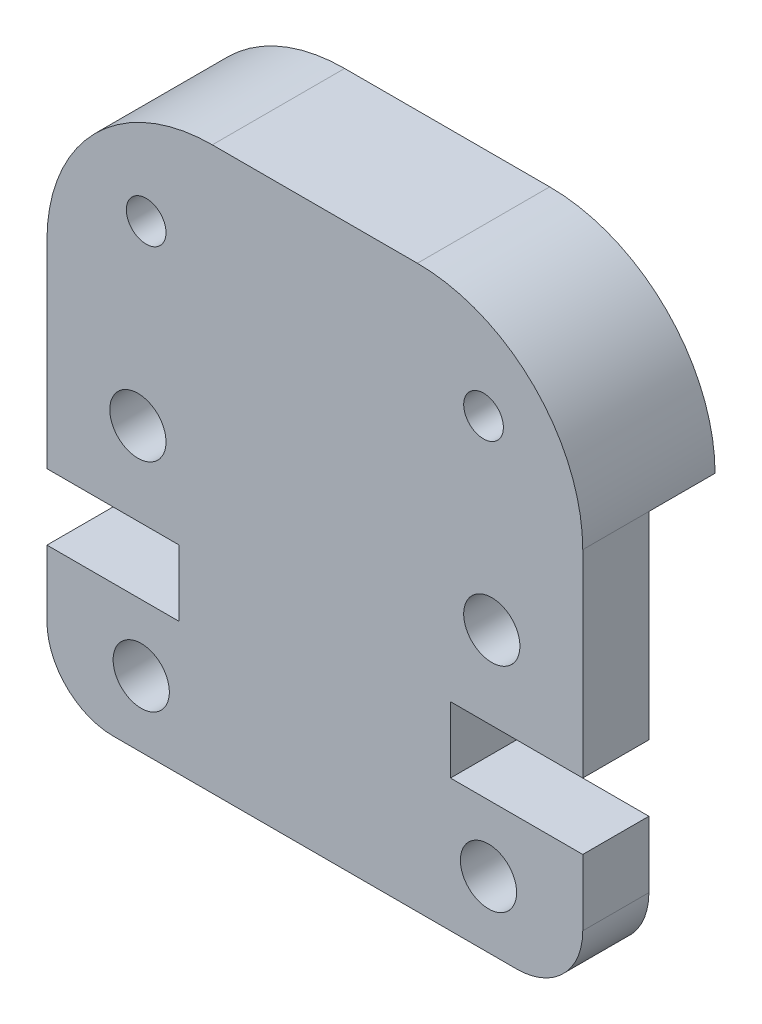
SolidWorks part; units mm, degrees
ref_plane "Front Plane" through (0, 0, 0) normal (0, 0, 1) x (1, 0, 0)
ref_plane "Top Plane" through (0, 0, 0) normal (0, 1, 0) x (1, 0, 0)
ref_plane "Right Plane" through (0, 0, 0) normal (1, 0, 0) x (0, 0, -1)
sketch "Sketch1" plane through (0, 0, 0) normal (0, 0, 1) x (1, 0, 0)
  line L0 (0, 16.98) -> (0, 0) construction
  line L1 (3.1, 16.98) -> (-3.1, 16.98)
  line L2 (6.1, 0) -> (-6.1, 0)
  line L3 (-8.1, 6) -> (-4.1, 6)
  line L4 (-4.1, 6) -> (-4.1, 4)
  line L5 (-4.1, 4) -> (-8.1, 4)
  line L6 (-8.1, 2) -> (-8.1, 4)
  line L7 (8.1, 11.98) -> (8.1, 6)
  line L8 (-8.1, 11.98) -> (-8.1, 6)
  line L24 (8.1, 2) -> (8.1, 4)
  line L27 (4.1, 4) -> (8.1, 4)
  line L30 (4.1, 6) -> (4.1, 4)
  line L31 (8.1, 6) -> (4.1, 6)
  circle A0 centre (-5.25, 2) radius 0.85
  circle A1 centre (-5.1, 13.98) radius 0.6
  arc A2 (-8.1, 11.98) -> (-3.1, 16.98) centre (-3.1, 11.98) cw
  arc A3 (-6.1, 0) -> (-8.1, 2) centre (-6.1, 2) cw
  circle A4 centre (-5.35, 8.5) radius 0.85
  circle A10 centre (5.35, 8.5) radius 0.85
  arc A12 (6.1, 0) -> (8.1, 2) centre (6.1, 2) ccw
  arc A14 (8.1, 11.98) -> (3.1, 16.98) centre (3.1, 11.98) ccw
  circle A16 centre (5.1, 13.98) radius 0.6
  circle A18 centre (5.25, 2) radius 0.85
  dimension "D1" = 1.7
  dimension "D2" = 1.2
  dimension "D3" = 16.98
  dimension "D4" = 2
  dimension "D5" = 5
  dimension "D6" = 6.1
  dimension "D7" = 3
  dimension "D8" = 3
  dimension "D9" = 2.75
  dimension "D10" = 8.5
extrude "Boss-Extrude1" add sketch "Sketch1" along normal blind 4
sketch "Sketch2" plane through (0, 0, 0) normal (0, 0, 1) x (1, 0, 0)
  line L0 (-8.1, 0) -> (8.1, 0)
  line L1 (8.1, 0) -> (8.1, 11.98)
  line L2 (8.1, 11.98) -> (-8.1, 11.98)
  line L3 (-8.1, 11.98) -> (-8.1, 0)
extrude "Cut-Extrude1" cut sketch "Sketch2" along normal blind 2
equation "\"D6@Sketch1\"= ( \"fingerWidth@parametersSketch@prostheticParameters.SLDPRT\" - 4 ) / 2'Finger Width - Radius"
equation "\"D3@Sketch1\"= ( \"HL@parametersSketch@prostheticParameters.SLDPRT\" * 0.108 ) - 3 'DIP Legth-Sil. Sh. DIP"
equation "\"D1@Sketch1\"= 1.5 + \"tol1@parametersSketch@prostheticParameters.SLDPRT\""
equation "\"D2@Sketch1\"= 1 + \"tol1@parametersSketch@prostheticParameters.SLDPRT\""
